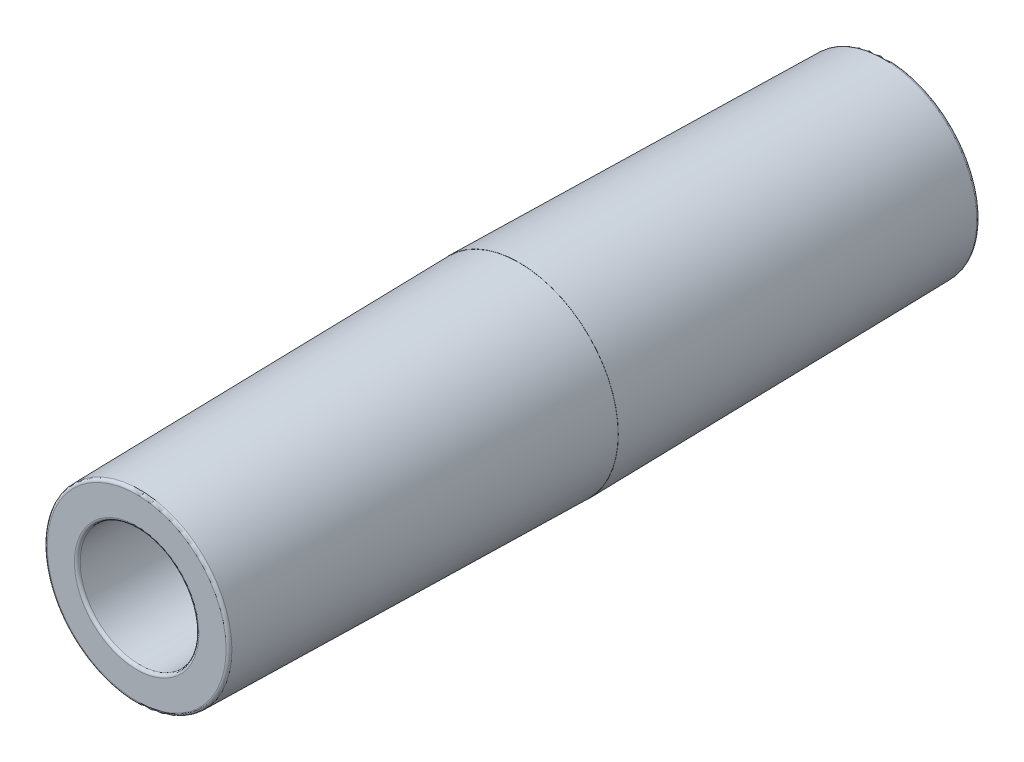
SolidWorks part; units mm, degrees
material "ABS"
ref_plane "Front Plane" through (0, 0, 0) normal (0, 0, 1) x (1, 0, 0)
ref_plane "Top Plane" through (0, 0, 0) normal (0, 1, 0) x (1, 0, 0)
ref_plane "Right Plane" through (0, 0, 0) normal (1, 0, 0) x (0, 0, -1)
sketch "Sketch1" plane through (0, 0, 0) normal (0, 1, 0) x (1, 0, 0)
  line L0 (5.1263, 31.75) -> (4.8514, 0)
  line L1 (4.8514, 0) -> (4.8387, 0)
  line L2 (4.8387, 0) -> (5.1247, -33.02)
  line L3 (5.1247, -33.02) -> (7.9707, -33.02)
  line L4 (7.9707, -33.02) -> (8.5471, 0)
  line L5 (8.5471, 0) -> (8.5598, 0)
  line L6 (8.5598, 0) -> (8.0056, 31.75)
  line L7 (8.0056, 31.75) -> (5.1263, 31.75)
  line L8 (0, 31.753) -> (0, -33.0239) construction
  line L9 (0, 0) -> (10.2056, 0) construction
  dimension "D1" = 64.77
  dimension "D2" = 9.6774
  dimension "D3" = 4.8514
  dimension "D4" = 5.1247
  dimension "D5" = 5.1263
  dimension "D6" = 17.0942
  dimension "D7" = 31.75
  dimension "D10" = 91
  dimension "D11" = 91
revolve "Revolve1" add sketch "Sketch1" angle 360 about L8
fillet "Fillet1" radius 0.254 4 edges at (5.1263, 0, -31.75) (8.0056, 0, -31.75) (5.1247, 0, 33.02) (7.9707, 0, 33.02)
